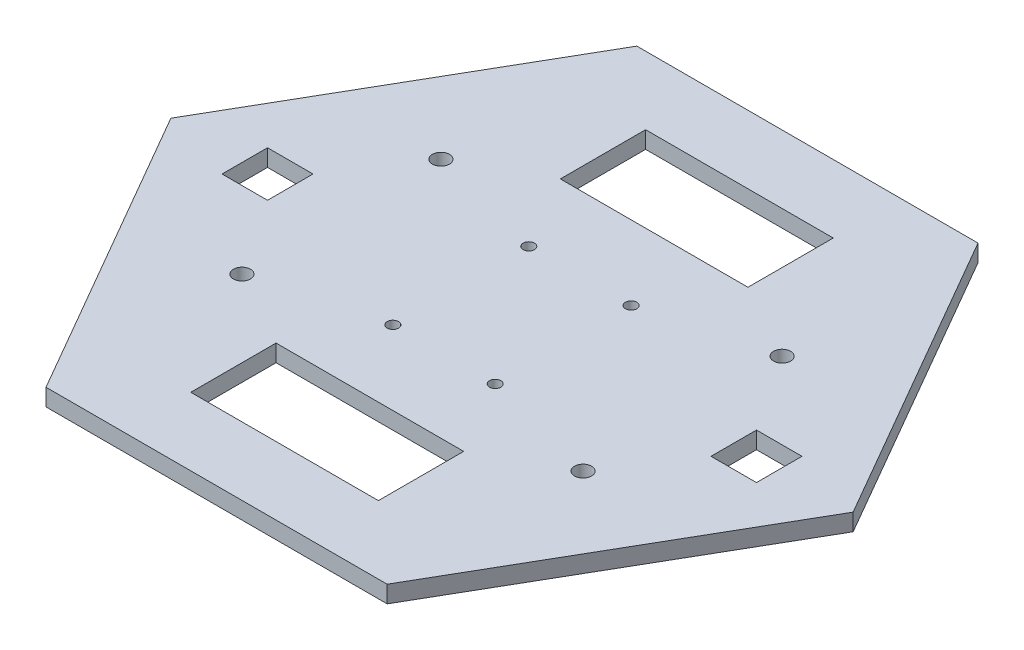
SolidWorks part; units mm, degrees
ref_plane "Alzado" through (0, 0, 0) normal (0, 0, 1) x (1, 0, 0)
ref_plane "Planta" through (0, 0, 0) normal (0, 1, 0) x (1, 0, 0)
ref_plane "Vista lateral" through (0, 0, 0) normal (1, 0, 0) x (0, 0, -1)
sketch "Croquis1" plane through (0, 0, 0) normal (0, 1, 0) x (1, 0, 0)
  line L1 (-60, 0) -> (-30, -51.9615)
  line L2 (-30, -51.9615) -> (30, -51.9615)
  line L3 (30, -51.9615) -> (60, 0)
  line L4 (60, 0) -> (30, 51.9615)
  line L5 (30, 51.9615) -> (-30, 51.9615)
  line L6 (-30, 51.9615) -> (-60, 0)
  circle A0 centre (0, 0) radius 51.9615 construction
  dimension "D1" = 120
extrude "Saliente-Extruir1" add sketch "Croquis1" along normal blind 3
sketch "Croquis3" plane through (0, 3, 0) normal (0, 1, 0) x (1, 0, 0)
  line L0 (0, 0) -> (-73.3513, 0) construction
  line L1 (-16.5, -25) -> (16.5, -25)
  line L2 (-16.5, -25) -> (-16.5, -40)
  line L3 (-16.5, -40) -> (16.5, -40)
  line L4 (16.5, -25) -> (16.5, -40)
  line L5 (-16.5, -25) -> (16.5, -40) construction
  line L6 (-16.5, -40) -> (16.5, -25) construction
  line L7 (-16.5, 40) -> (16.5, 40)
  line L8 (-16.5, 40) -> (-16.5, 25)
  line L9 (-16.5, 25) -> (16.5, 25)
  line L10 (16.5, 40) -> (16.5, 25)
  line L11 (-16.5, 40) -> (16.5, 25) construction
  line L12 (-16.5, 25) -> (16.5, 40) construction
  line L13 (0, 0) -> (0, 15) construction
  point P0 (0, -32.5)
  point P5 (0, 32.5)
  point P13 (-16.5, 42.4789)
  dimension "D1" = 33
  dimension "D2" = 15
  dimension "D3" = 15
  dimension "D4" = 33
  dimension "D5" = 50
extrude "Cortar-Extruir1" cut sketch "Croquis3" against normal through all
sketch "Croquis4" plane through (0, 3, 0) normal (0, 1, 0) x (1, 0, 0)
  line L0 (16.5, -25) -> (-16.5, -25) construction
  line L1 (0, 0) -> (0, -58.4022) construction
  line L2 (0, 0) -> (-23.1523, 0) construction
  circle A0 centre (-9, -11.95) radius 1
  circle A1 centre (9, -11.95) radius 1
  circle A2 centre (9, 11.95) radius 1
  circle A3 centre (-9, 11.95) radius 1
  dimension "D1" = 2
  dimension "D2" = 13.05
  dimension "D3" = 18
extrude "Cortar-Extruir2" cut sketch "Croquis4" against normal through all
sketch "Croquis5" plane through (0, 3, 0) normal (0, 1, 0) x (1, 0, 0)
  line L0 (0, 0) -> (-77.2518, 0) construction
  line L5 (47, -4) -> (39, 4) construction
  line L6 (-47, 4) -> (-39, 4)
  line L7 (0, 0) -> (0, -86.0106) construction
  line L8 (-47, 4) -> (-47, -4)
  line L9 (-47, -4) -> (-39, -4)
  line L14 (-39, 4) -> (-39, -4)
  line L15 (-47, 4) -> (-39, -4) construction
  line L16 (-47, -4) -> (-39, 4) construction
  line L17 (47, 4) -> (39, -4) construction
  line L26 (39, 4) -> (39, -4)
  line L27 (47, -4) -> (39, -4)
  line L28 (47, 4) -> (47, -4)
  line L29 (47, 4) -> (39, 4)
  point P0 (-43, 0)
  point P13 (43, 0)
  dimension "D1" = 8
  dimension "D2" = 8
  dimension "D3" = 43
extrude "Cortar-Extruir3" cut sketch "Croquis5" against normal through all
sketch "Croquis6" plane through (0, 3, 0) normal (0, 1, 0) x (1, 0, 0)
  line L0 (0, 0) -> (0, 63.7682) construction
  line L1 (0, 0) -> (-25.6871, 0) construction
  circle A4 centre (-30, -17.5) radius 1.5
  circle A5 centre (-30, 17.5) radius 1.5
  circle A6 centre (30, 17.5) radius 1.5
  circle A7 centre (30, -17.5) radius 1.5
  dimension "D1" = 3
  dimension "D2" = 35
  dimension "D3" = 35
  dimension "D4" = 60
  dimension "D5" = 60
extrude "Cortar-Extruir4" cut sketch "Croquis6" against normal through all
